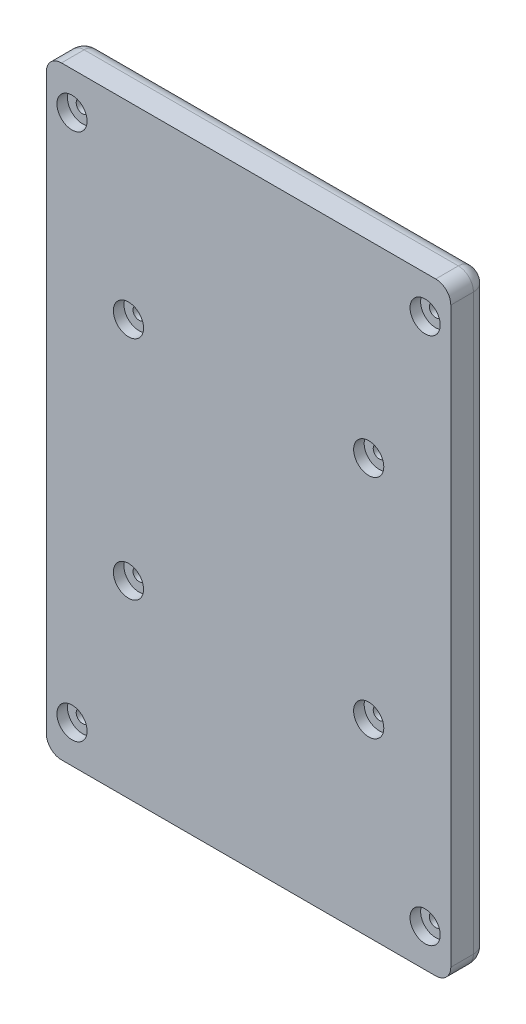
SolidWorks part; units mm, degrees
material "Roble"
ref_plane "Alzado" through (0, 0, 0) normal (0, 0, 1) x (1, 0, 0)
ref_plane "Planta" through (0, 0, 0) normal (0, 1, 0) x (1, 0, 0)
ref_plane "Vista lateral" through (0, 0, 0) normal (1, 0, 0) x (0, 0, -1)
sketch "Croquis1" plane through (0, 0, 0) normal (0, 0, 1) x (1, 0, 0)
  line L0 (213.605, 400) -> (213.605, 0) construction
  line L1 (0, 0) -> (268, 0)
  line L2 (0, 0) -> (0, 400)
  line L3 (0, 400) -> (268, 400)
  line L4 (268, 0) -> (268, 400)
  line L5 (54.405, 400) -> (54.405, 0) construction
  line L6 (268, 275) -> (0, 275) construction
  line L7 (268, 125) -> (0, 125) construction
  line L8 (268, 200) -> (-20.6758, 200) construction
  circle A0 centre (54.405, 275) radius 4
  circle A1 centre (213.605, 275) radius 4
  circle A2 centre (213.605, 125) radius 4
  circle A3 centre (54.405, 125) radius 4
  point P13 (54.405, 275)
  point P14 (213.605, 275)
  point P15 (213.605, 125)
  point P16 (54.405, 125)
  dimension "D7" = 8
  dimension "D1" = 400
  dimension "D2" = 268
  dimension "D3" = 54.395
  dimension "D4" = 159.2
  dimension "D5" = 75
  dimension "D6" = 75
extrude "Saliente-Extruir1" add sketch "Croquis1" along normal blind 25
sketch "Croquis2" plane through (0, 0, 25) normal (0, 0, 1) x (1, 0, 0)
  circle A0 centre (54.405, 275) radius 10
  circle A1 centre (213.605, 275) radius 10
  circle A2 centre (213.605, 125) radius 10
  circle A3 centre (54.405, 125) radius 10
  dimension "D1" = 20
extrude "Cortar-Extruir1" cut sketch "Croquis2" against normal blind 7
fillet "Redondeo1" radius 10 4 edges at (268, 0, 12.5) (0, 0, 12.5) (268, 400, 12.5) (0, 400, 12.5)
fillet "Redondeo2" radius 10 8 edges at (265.0711, 397.0711, 0) (268, 200, 0) (265.0711, 2.9289, 0) (134, 0, 0) (2.9289, 2.9289, 0) (0, 200, 0) (2.9289, 397.0711, 0) (134, 400, 0)
sketch "Croquis3" plane through (0, 0, 25) normal (0, 0, 1) x (1, 0, 0)
  line L0 (17, 429.1476) -> (17, -51.4055) construction
  line L1 (251, 429.1476) -> (251, -51.4055) construction
  line L2 (-25.3821, 25) -> (318.2324, 25) construction
  line L3 (-39.3296, 375) -> (297.9452, 375) construction
  line L4 (0, 390) -> (0, 10) construction
  line L5 (10, 0) -> (258, 0) construction
  line L6 (268, 10) -> (268, 390) construction
  line L7 (258, 400) -> (10, 400) construction
  circle A0 centre (17, 375) radius 10
  circle A1 centre (251, 375) radius 10
  circle A2 centre (251, 25) radius 10
  circle A3 centre (17, 25) radius 10
  circle A4 centre (54.405, 125) radius 10 construction
  point P16 (17, 375)
  point P17 (251, 375)
  point P18 (251, 25)
  point P19 (17, 25)
  dimension "D1" = 17
  dimension "D2" = 25
  dimension "D3" = 17
  dimension "D4" = 25
extrude "Cortar-Extruir2" cut sketch "Croquis3" against normal blind 7
hole_wizard "Taladro de margen para 5/161" positions "Croquis5" profile "Croquis6" hole size "5/16" standard "Ansi Inch" end condition up to next
sketch "Croquis5" plane through (0, 0, 18) normal (0, 0, 1) x (1, 0, 0)
  point P0 (17, 25)
  point P3 (251, 25)
  point P6 (251, 375)
  point P9 (17, 375)
sketch "Croquis6" plane through (17, 25, 18) normal (1, 0, 0) x (0, -1, 0)
  line L0 (0, 0) -> (0, 18)
  line L1 (0, 18) -> (4.2164, 18)
  line L2 (4.2164, 18) -> (4.2164, 0)
  line L5 (4.2164, 0) -> (0, 0)
  line L11 (0, -6.35) -> (0, 107.95) construction
  dimension "Diámetro de taladro hasta el siguiente" = 8.4328
  dimension "Profundidad de taladro hasta el siguiente" = 18
